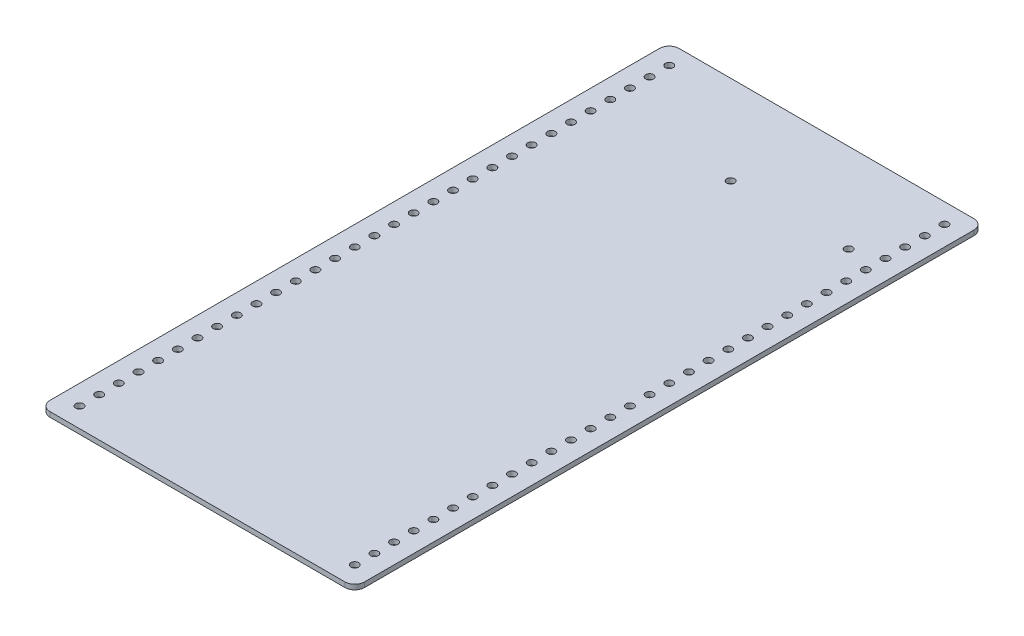
SolidWorks part; units mm, degrees
ref_plane "Front Plane" through (0, 0, 0) normal (0, 0, 1) x (1, 0, 0)
ref_plane "Top Plane" through (0, 0, 0) normal (0, 1, 0) x (1, 0, 0)
ref_plane "Right Plane" through (0, 0, 0) normal (1, 0, 0) x (0, 0, -1)
sketch "Sketch1" plane through (0, 0, 0) normal (0, 1, 0) x (1, 0, 0)
  line L1 (-77.8898, 288.009) -> (112.6102, 288.009)
  line L2 (-84.2398, 281.659) -> (-84.2398, -112.041)
  line L3 (-77.8898, -118.391) -> (112.6102, -118.391)
  line L4 (118.9602, 281.659) -> (118.9602, -112.041)
  arc A0 (-84.2398, -112.041) -> (-77.8898, -118.391) centre (-77.8898, -112.041) ccw
  arc A1 (112.6102, -118.391) -> (118.9602, -112.041) centre (112.6102, -112.041) ccw
  arc A2 (112.6102, 288.009) -> (118.9602, 281.659) centre (112.6102, 281.659) cw
  arc A3 (-77.8898, 288.009) -> (-84.2398, 281.659) centre (-77.8898, 281.659) ccw
  point P6 (-84.2398, -118.391)
  point P9 (118.9602, -118.391)
  point P14 (-84.2398, 288.009)
  dimension "D3" = 6.35
  dimension "D1" = 203.2
  dimension "D2" = 406.4
extrude "Boss-Extrude1" add sketch "Sketch1" along normal blind 3.175
sketch "Sketch3" plane through (0, 3.175, 0) normal (0, 1, 0) x (1, 0, 0)
  line L0 (118.9602, -112.041) -> (118.9602, 281.659) construction
  line L1 (112.6102, 288.009) -> (-77.8898, 288.009) construction
  line L2 (-84.2398, 281.659) -> (-84.2398, -112.041) construction
  circle A0 centre (-71.5398, 275.309) radius 2.5
  circle A1 centre (106.2602, 275.309) radius 2.5
  circle A2 centre (-71.5398, 262.609) radius 2.5
  circle A3 centre (106.2602, 262.609) radius 2.5
  circle A4 centre (-71.5398, 249.909) radius 2.5
  circle A5 centre (106.2602, 249.909) radius 2.5
  circle A6 centre (-71.5398, 237.209) radius 2.5
  circle A7 centre (106.2602, 237.209) radius 2.5
  circle A8 centre (-71.5398, 224.509) radius 2.5
  circle A9 centre (106.2602, 224.509) radius 2.5
  circle A10 centre (-71.5398, 211.809) radius 2.5
  circle A11 centre (106.2602, 211.809) radius 2.5
  circle A12 centre (-71.5398, 199.109) radius 2.5
  circle A13 centre (106.2602, 199.109) radius 2.5
  circle A14 centre (-71.5398, 186.409) radius 2.5
  circle A15 centre (106.2602, 186.409) radius 2.5
  circle A16 centre (-71.5398, 173.709) radius 2.5
  circle A17 centre (106.2602, 173.709) radius 2.5
  circle A18 centre (-71.5398, 161.009) radius 2.5
  circle A19 centre (106.2602, 161.009) radius 2.5
  circle A20 centre (-71.5398, 148.309) radius 2.5
  circle A21 centre (106.2602, 148.309) radius 2.5
  circle A22 centre (-71.5398, 135.609) radius 2.5
  circle A23 centre (106.2602, 135.609) radius 2.5
  circle A24 centre (-71.5398, 122.909) radius 2.5
  circle A25 centre (106.2602, 122.909) radius 2.5
  circle A26 centre (-71.5398, 110.209) radius 2.5
  circle A27 centre (106.2602, 110.209) radius 2.5
  circle A28 centre (-71.5398, 97.509) radius 2.5
  circle A29 centre (106.2602, 97.509) radius 2.5
  circle A30 centre (-71.5398, 84.809) radius 2.5
  circle A31 centre (106.2602, 84.809) radius 2.5
  circle A32 centre (-71.5398, 72.109) radius 2.5
  circle A33 centre (106.2602, 72.109) radius 2.5
  circle A34 centre (-71.5398, 59.409) radius 2.5
  circle A35 centre (106.2602, 59.409) radius 2.5
  circle A36 centre (-71.5398, 46.709) radius 2.5
  circle A37 centre (106.2602, 46.709) radius 2.5
  circle A38 centre (-71.5398, 34.009) radius 2.5
  circle A39 centre (106.2602, 34.009) radius 2.5
  circle A40 centre (-71.5398, 21.309) radius 2.5
  circle A41 centre (106.2602, 21.309) radius 2.5
  circle A42 centre (-71.5398, 8.609) radius 2.5
  circle A43 centre (106.2602, 8.609) radius 2.5
  circle A44 centre (-71.5398, -4.091) radius 2.5
  circle A45 centre (106.2602, -4.091) radius 2.5
  circle A46 centre (-71.5398, -16.791) radius 2.5
  circle A47 centre (106.2602, -16.791) radius 2.5
  circle A48 centre (-71.5398, -29.491) radius 2.5
  circle A49 centre (106.2602, -29.491) radius 2.5
  circle A50 centre (-71.5398, -42.191) radius 2.5
  circle A51 centre (106.2602, -42.191) radius 2.5
  circle A52 centre (-71.5398, -54.891) radius 2.5
  circle A53 centre (106.2602, -54.891) radius 2.5
  circle A54 centre (-71.5398, -67.591) radius 2.5
  circle A55 centre (106.2602, -67.591) radius 2.5
  circle A56 centre (-71.5398, -80.291) radius 2.5
  circle A57 centre (106.2602, -80.291) radius 2.5
  circle A58 centre (-71.5398, -92.991) radius 2.5
  circle A59 centre (106.2602, -92.991) radius 2.5
  circle A60 centre (-71.5398, -105.691) radius 2.5
  circle A61 centre (106.2602, -105.691) radius 2.5
  dimension "D1" = 5
  dimension "D2" = 5
  dimension "D3" = 12.7
  dimension "D4" = 12.7
  dimension "D5" = 12.7
  dimension "D6" = 12.7
  dimension "D7" = 31
extrude "Cut-Extrude2" cut sketch "Sketch3" against normal through all
sketch "Sketch7" plane through (0, 3.175, 0) normal (0, 1, 0) x (1, 0, 0)
  circle A0 centre (89.0759, 230.5666) radius 2.5 construction
  circle A1 centre (12.8759, 230.5666) radius 2.5 construction
  circle A2 centre (89.0759, 230.5666) radius 2.5
  circle A3 centre (12.8759, 230.5666) radius 2.5
extrude "Cut-Extrude5" cut sketch "Sketch7" against normal through all
